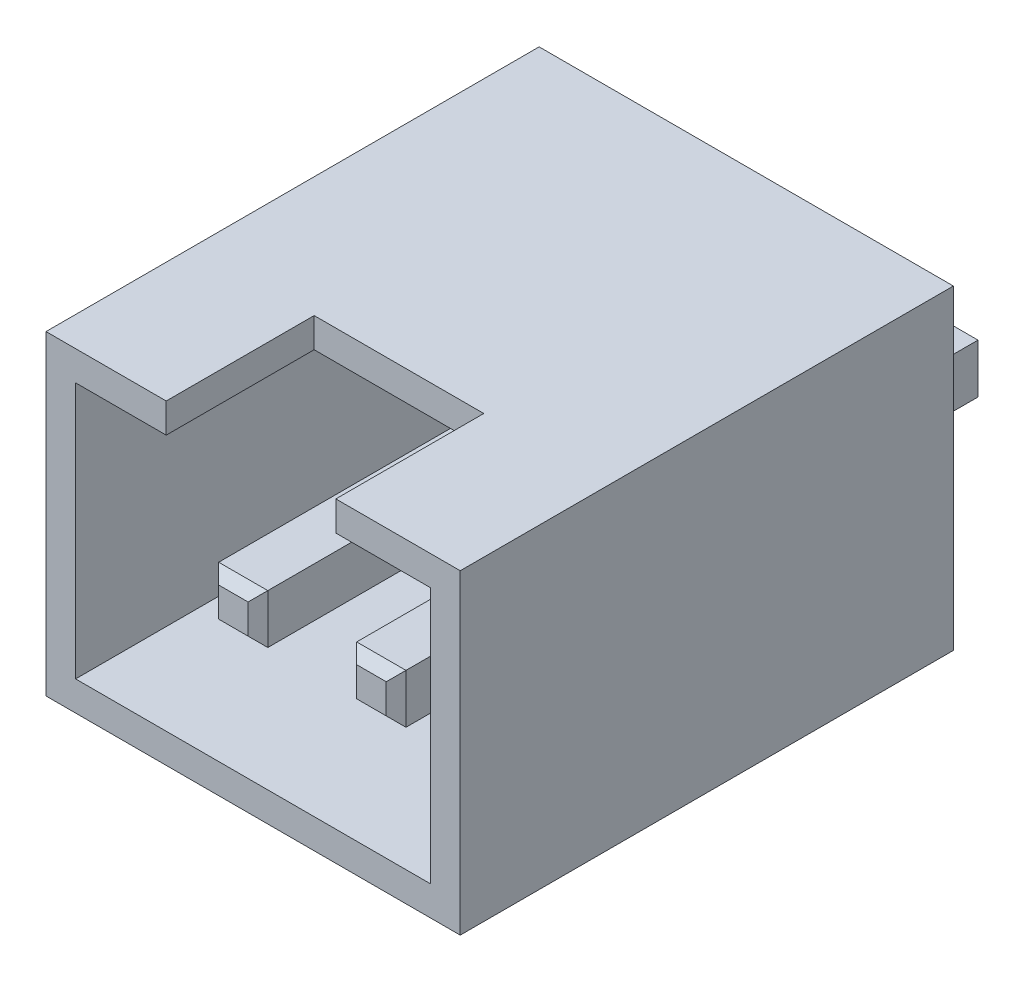
SolidWorks part; units mm, degrees
ref_plane "前视基准面" through (0, 0, 0) normal (0, 0, 1) x (1, 0, 0)
ref_plane "上视基准面" through (0, 0, 0) normal (0, 1, 0) x (1, 0, 0)
ref_plane "右视基准面" through (0, 0, 0) normal (1, 0, 0) x (0, 0, -1)
sketch "草图1" plane through (0, 0, 0) normal (0, 0, 1) x (1, 0, 0)
  line L1 (-2.1, 1.6) -> (2.1, 1.6)
  line L2 (-2.1, 1.6) -> (-2.1, -1.6)
  line L3 (-2.1, -1.6) -> (2.1, -1.6)
  line L4 (2.1, 1.6) -> (2.1, -1.6)
  line L5 (-2.1, 1.6) -> (2.1, -1.6) construction
  line L6 (-2.1, -1.6) -> (2.1, 1.6) construction
  point P0 (0, 0)
extrude "凸台-拉伸1" add sketch "草图1" along normal blind 5
sketch "草图2" plane through (0, 0, 5) normal (0, 0, 1) x (1, 0, 0)
  line L1 (-1.8, 1.3) -> (1.8, 1.3)
  line L2 (-1.8, 1.3) -> (-1.8, -1.3)
  line L3 (-1.8, -1.3) -> (1.8, -1.3)
  line L4 (1.8, 1.3) -> (1.8, -1.3)
  line L5 (-1.8, 1.3) -> (1.8, -1.3) construction
  line L6 (-1.8, -1.3) -> (1.8, 1.3) construction
  point P0 (0, 0)
extrude "切除-拉伸2" cut sketch "草图2" against normal blind 4.5
sketch "草图10" plane through (0, 0, 5) normal (0, 0, 1) x (1, 0, 0)
  line L0 (2.1, 1.6) -> (-2.1, 1.6) construction
  line L1 (-0.8811, 1.6) -> (0.8388, 1.6)
  line L2 (-0.8811, 1.6) -> (-0.8811, 1.3)
  line L3 (-0.8811, 1.3) -> (0.8388, 1.3)
  line L4 (0.8388, 1.6) -> (0.8388, 1.3)
  line L5 (1.8, 1.3) -> (-1.8, 1.3) construction
extrude "切除-拉伸6" cut sketch "草图10" against normal blind 1.5
sketch "草图12" plane through (0, 0, 0.5) normal (0, 0, 1) x (1, 0, 0)
  line L5 (-0.949, -0.15) -> (-0.451, -0.15)
  line L6 (-0.949, -0.15) -> (-0.949, -0.65)
  line L7 (-0.949, -0.65) -> (-0.451, -0.65)
  line L8 (-0.451, -0.15) -> (-0.451, -0.65)
  line L9 (-0.949, -0.15) -> (-0.451, -0.65) construction
  line L10 (-0.949, -0.65) -> (-0.451, -0.15) construction
  line L11 (0.4502, -0.15) -> (0.9498, -0.15)
  line L12 (0.4502, -0.15) -> (0.4502, -0.65)
  line L13 (0.4502, -0.65) -> (0.9498, -0.65)
  line L14 (0.9498, -0.15) -> (0.9498, -0.65)
  line L15 (0.4502, -0.15) -> (0.9498, -0.65) construction
  line L16 (0.4502, -0.65) -> (0.9498, -0.15) construction
extrude "凸台-拉伸2" add sketch "草图12" along normal blind 4 and the other way blind 2
chamfer "倒角2" distance 0.1 angle 45 8 edges at (0.7, -0.65, 4.5) (0.4502, -0.4, 4.5) (0.7, -0.15, 4.5) (0.9498, -0.4, 4.5) (-0.7, -0.65, 4.5) (-0.949, -0.4, 4.5) (-0.7, -0.15, 4.5) (-0.451, -0.4, 4.5)
chamfer "倒角3" distance 0.1 angle 45 8 edges at (0.7, -0.15, -1.5) (0.4502, -0.4, -1.5) (0.7, -0.65, -1.5) (0.9498, -0.4, -1.5) (-0.7, -0.15, -1.5) (-0.949, -0.4, -1.5) (-0.7, -0.65, -1.5) (-0.451, -0.4, -1.5)
